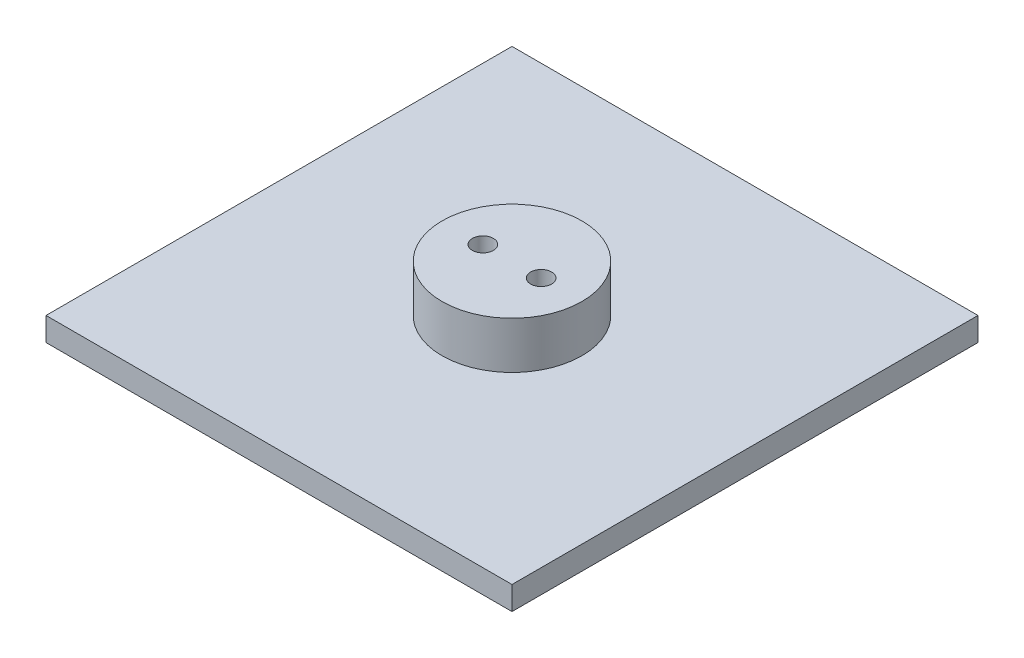
SolidWorks part; units mm, degrees
ref_plane "Front Plane" through (0, 0, 0) normal (0, 0, 1) x (1, 0, 0)
ref_plane "Top Plane" through (0, 0, 0) normal (0, 1, 0) x (1, 0, 0)
ref_plane "Right Plane" through (0, 0, 0) normal (1, 0, 0) x (0, 0, -1)
sketch "Sketch1" plane through (0, 0, 0) normal (0, 1, 0) x (1, 0, 0)
  line L1 (0, 0) -> (79.375, 0)
  line L2 (0, 0) -> (0, 79.375)
  line L3 (0, 79.375) -> (79.375, 79.375)
  line L4 (79.375, 0) -> (79.375, 79.375)
  dimension "D1" = 79.375
extrude "Boss-Extrude1" add sketch "Sketch1" along normal blind 4
sketch "Sketch2" plane through (0, 4, 0) normal (0, 1, 0) x (1, 0, 0)
  line L0 (0, 0) -> (79.375, 0) construction
  line L9 (0, 0) -> (39.6875, 0) construction
  line L14 (0, 0) -> (0, 39.6875) construction
  line L15 (0, 39.6875) -> (39.6875, 39.6875) construction
  line L16 (39.6875, 0) -> (39.6875, 39.6875) construction
  circle A0 centre (39.6875, 39.6875) radius 11.9062
  point P7 (39.6875, 0)
  dimension "D1" = 23.8125
extrude "Boss-Extrude2" add sketch "Sketch2" along normal blind 8
sketch "Sketch3" plane through (0, 12, 0) normal (0, 1, 0) x (1, 0, 0)
  line L0 (0, 39.6875) -> (79.375, 39.6875) construction
  line L1 (0, 79.375) -> (0, 0) construction
  line L2 (79.375, 0) -> (79.375, 79.375) construction
  line L3 (36.5125, 39.6875) -> (42.8625, 39.6875) construction
  line L4 (32.9406, 39.6875) -> (46.4344, 39.6875) construction
  line L5 (32.9406, 39.6875) -> (32.9406, 49.4976) construction
  line L6 (46.4344, 39.6875) -> (46.4344, 49.4976) construction
  line L7 (32.9406, 49.4976) -> (46.4344, 49.4976) construction
  line L8 (36.5125, 39.6875) -> (36.5125, 49.4976) construction
  line L9 (42.8625, 39.6875) -> (42.8625, 49.4976) construction
  line L10 (36.5125, 49.4976) -> (42.8625, 49.4976) construction
  circle A0 centre (34.7266, 39.6875) radius 1.7859
  circle A1 centre (44.6484, 39.6875) radius 1.7859
  circle A3 centre (39.6875, 39.6875) radius 11.9062 construction
  point P10 (39.6875, 49.4976)
  point P12 (36.5125, 46.7011)
  point P18 (32.9406, 49.4976)
  point P22 (39.6875, 39.6875)
  dimension "D1" = 6.35
  dimension "D2" = 13.4937
extrude "Cut-Extrude1" cut sketch "Sketch3" against normal up to surface (12 mm away) up to face at (39.6875, 0, -39.6875)
